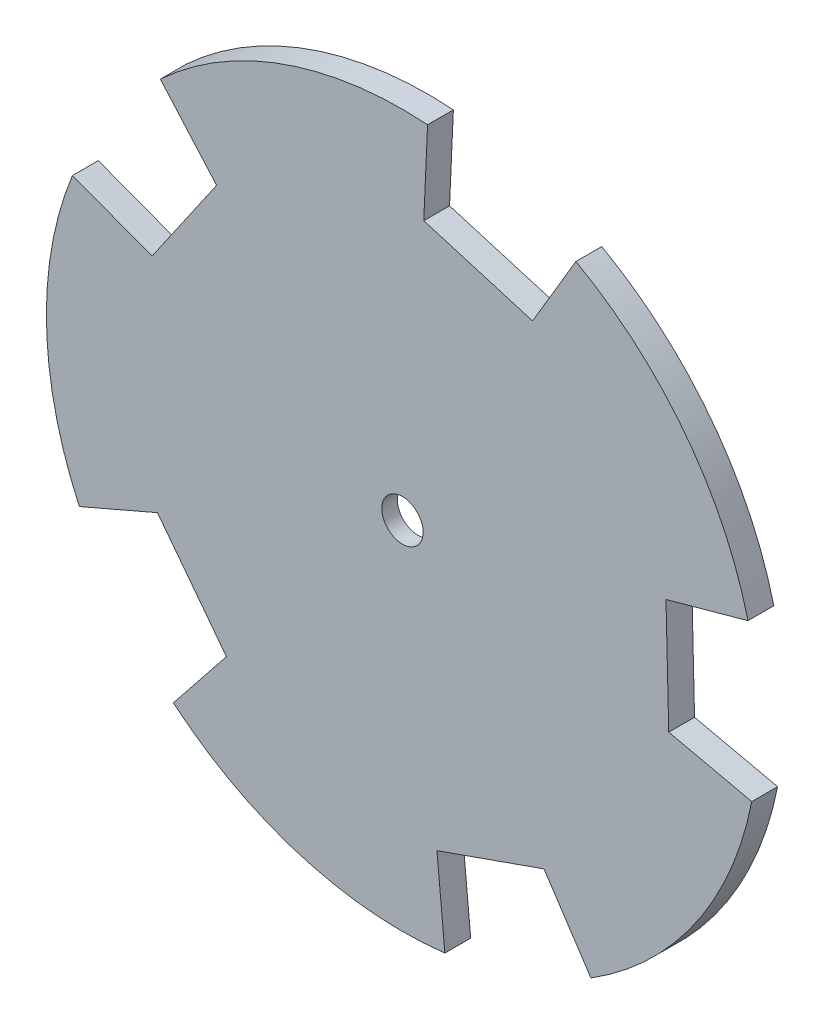
SolidWorks part; units mm, degrees
ref_plane "Front Plane" through (0, 0, 0) normal (0, 0, 1) x (1, 0, 0)
ref_plane "Top Plane" through (0, 0, 0) normal (0, 1, 0) x (1, 0, 0)
ref_plane "Right Plane" through (0, 0, 0) normal (1, 0, 0) x (0, 0, -1)
sketch "Sketch1" plane through (0, 0, 0) normal (0, 0, 1) x (1, 0, 0)
  line L18 (-23.4602, 25.2956) -> (-18.0108, 19.1066)
  line L19 (-18.0108, 19.1066) -> (-24.2571, 10.0521)
  line L20 (-24.2571, 10.0521) -> (-31.9779, 12.9486)
  line L21 (-31.3072, -14.4952) -> (-23.7371, -11.225)
  line L22 (-23.7371, -11.225) -> (-17.056, -19.9636)
  line L23 (-17.056, -19.9636) -> (-22.1965, -26.4114)
  line L24 (4.1113, -34.2542) -> (3.3405, -26.044)
  line L25 (3.3405, -26.044) -> (13.7159, -22.3903)
  line L26 (13.7159, -22.3903) -> (18.2597, -29.2717)
  line L27 (33.8481, -6.675) -> (25.8016, -4.8711)
  line L28 (25.8016, -4.8711) -> (25.5329, 6.1257)
  line L29 (25.5329, 6.1257) -> (33.4816, 8.3205)
  line L33 (16.808, 30.1288) -> (12.6058, 23.0336)
  line L34 (12.6058, 23.0336) -> (2.0643, 26.1761)
  line L35 (2.0643, 26.1761) -> (2.4331, 34.4141)
  line L36 (-23.4602, 25.2956) -> (-18.0108, 19.1066)
  line L37 (-18.0108, 19.1066) -> (-24.2571, 10.0521)
  line L38 (-24.2571, 10.0521) -> (-31.9779, 12.9486)
  line L39 (-31.3072, -14.4952) -> (-23.7371, -11.225)
  line L40 (-23.7371, -11.225) -> (-17.056, -19.9636)
  line L41 (-17.056, -19.9636) -> (-22.1965, -26.4114)
  line L42 (4.1113, -34.2542) -> (3.3405, -26.044)
  line L43 (3.3405, -26.044) -> (13.7159, -22.3903)
  line L44 (13.7159, -22.3903) -> (18.2597, -29.2717)
  line L45 (33.8481, -6.675) -> (25.8016, -4.8711)
  line L46 (25.8016, -4.8711) -> (25.5329, 6.1257)
  line L47 (25.5329, 6.1257) -> (33.4816, 8.3205)
  line L51 (16.808, 30.1288) -> (12.6058, 23.0336)
  line L52 (12.6058, 23.0336) -> (2.0643, 26.1761)
  line L53 (2.0643, 26.1761) -> (2.4331, 34.4141)
  arc A6 (-31.9779, 12.9486) -> (-31.3072, -14.4952) centre (0, 0) ccw
  arc A7 (-22.1965, -26.4114) -> (4.1113, -34.2542) centre (0, 0) ccw
  arc A8 (18.2597, -29.2717) -> (33.8481, -6.675) centre (0, 0) ccw
  arc A9 (33.4816, 8.3205) -> (16.808, 30.1288) centre (0, 0) ccw
  arc A11 (2.4331, 34.4141) -> (-23.4602, 25.2956) centre (0, 0) ccw
  arc A12 (-31.9779, 12.9486) -> (-31.3072, -14.4952) centre (0, 0) ccw
  arc A13 (-22.1965, -26.4114) -> (4.1113, -34.2542) centre (0, 0) ccw
  arc A14 (18.2597, -29.2717) -> (33.8481, -6.675) centre (0, 0) ccw
  arc A15 (33.4816, 8.3205) -> (16.808, 30.1288) centre (0, 0) ccw
  arc A17 (2.4331, 34.4141) -> (-23.4602, 25.2956) centre (0, 0) ccw
  dimension "D1" = 0
extrude "Boss-Extrude1" add sketch "Sketch1" along normal blind 1.5
sketch "Sketch2" plane through (0, 0, 0) normal (0, 0, -1) x (-1, 0, 0)
  line L18 (-2.4331, 34.4141) -> (-2.0643, 26.1761)
  line L19 (-2.0643, 26.1761) -> (-12.6058, 23.0336)
  line L20 (-12.6058, 23.0336) -> (-16.808, 30.1288)
  line L24 (-33.4816, 8.3205) -> (-25.5329, 6.1257)
  line L25 (-25.5329, 6.1257) -> (-25.8016, -4.8711)
  line L26 (-25.8016, -4.8711) -> (-33.8481, -6.675)
  line L27 (-18.2597, -29.2717) -> (-13.7159, -22.3903)
  line L28 (-13.7159, -22.3903) -> (-3.3405, -26.044)
  line L29 (-3.3405, -26.044) -> (-4.1113, -34.2542)
  line L30 (22.1965, -26.4114) -> (17.056, -19.9636)
  line L31 (17.056, -19.9636) -> (23.7371, -11.225)
  line L32 (23.7371, -11.225) -> (31.3072, -14.4952)
  line L33 (31.9779, 12.9486) -> (24.2571, 10.0521)
  line L34 (24.2571, 10.0521) -> (18.0108, 19.1066)
  line L35 (18.0108, 19.1066) -> (23.4602, 25.2956)
  line L36 (-2.4331, 34.4141) -> (-2.0643, 26.1761)
  line L37 (-2.0643, 26.1761) -> (-12.6058, 23.0336)
  line L38 (-12.6058, 23.0336) -> (-16.808, 30.1288)
  line L42 (-33.4816, 8.3205) -> (-25.5329, 6.1257)
  line L43 (-25.5329, 6.1257) -> (-25.8016, -4.8711)
  line L44 (-25.8016, -4.8711) -> (-33.8481, -6.675)
  line L45 (-18.2597, -29.2717) -> (-13.7159, -22.3903)
  line L46 (-13.7159, -22.3903) -> (-3.3405, -26.044)
  line L47 (-3.3405, -26.044) -> (-4.1113, -34.2542)
  line L48 (22.1965, -26.4114) -> (17.056, -19.9636)
  line L49 (17.056, -19.9636) -> (23.7371, -11.225)
  line L50 (23.7371, -11.225) -> (31.3072, -14.4952)
  line L51 (31.9779, 12.9486) -> (24.2571, 10.0521)
  line L52 (24.2571, 10.0521) -> (18.0108, 19.1066)
  line L53 (18.0108, 19.1066) -> (23.4602, 25.2956)
  circle A0 centre (0, 0) radius 3.875 construction
  circle A1 centre (0, 0) radius 3.875 construction
  circle A2 centre (0, 0) radius 4.075
  arc A6 (23.4602, 25.2956) -> (-2.4331, 34.4141) centre (0, 0) ccw
  arc A8 (-16.808, 30.1288) -> (-33.4816, 8.3205) centre (0, 0) ccw
  arc A9 (-33.8481, -6.675) -> (-18.2597, -29.2717) centre (0, 0) ccw
  arc A10 (-4.1113, -34.2542) -> (22.1965, -26.4114) centre (0, 0) ccw
  arc A11 (31.3072, -14.4952) -> (31.9779, 12.9486) centre (0, 0) ccw
  arc A12 (23.4602, 25.2956) -> (-2.4331, 34.4141) centre (0, 0) ccw
  arc A14 (-16.808, 30.1288) -> (-33.4816, 8.3205) centre (0, 0) ccw
  arc A15 (-33.8481, -6.675) -> (-18.2597, -29.2717) centre (0, 0) ccw
  arc A16 (-4.1113, -34.2542) -> (22.1965, -26.4114) centre (0, 0) ccw
  arc A17 (31.3072, -14.4952) -> (31.9779, 12.9486) centre (0, 0) ccw
  dimension "D1" = 0
  dimension "D2" = 0.2
extrude "Boss-Extrude2" add sketch "Sketch2" along normal up to surface (1 mm away)
sketch "Sketch3" plane through (0, 0, 0) normal (0, 0, -1) x (-1, 0, 0)
  circle A0 centre (0, 0) radius 2 construction
  circle A1 centre (0, 0) radius 2
extrude "Cut-Extrude1" cut sketch "Sketch3" against normal through all
